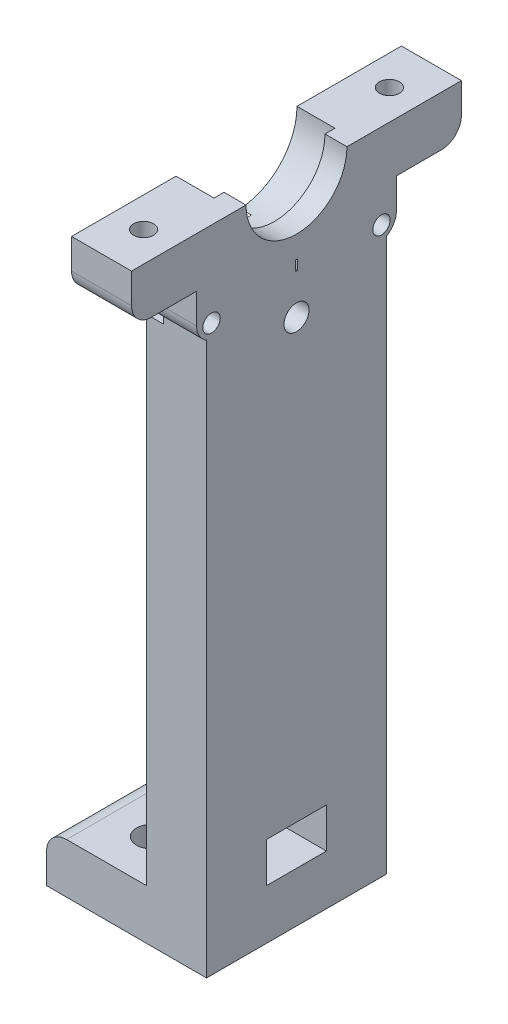
SolidWorks part; units mm, degrees
ref_plane "Front Plane" through (0, 0, 0) normal (0, 0, 1) x (1, 0, 0)
ref_plane "Top Plane" through (0, 0, 0) normal (0, 1, 0) x (1, 0, 0)
ref_plane "Right Plane" through (0, 0, 0) normal (1, 0, 0) x (0, 0, -1)
sketch "Sketch1" plane through (0, 0, 0) normal (0, 1, 0) x (1, 0, 0)
  circle A0 centre (0, 0) radius 17.45
  circle A1 centre (0, 0) radius 12.45
  dimension "D1" = 5
  dimension "D2" = 34.9
extrude "Boss-Extrude1" add sketch "Sketch1" along normal blind 8
sketch "Sketch2" plane through (0, 8, 0) normal (0, 1, 0) x (1, 0, 0)
  circle A0 centre (0, 0) radius 12.45
  circle A1 centre (0, 0) radius 20
  dimension "D1" = 40
extrude "Boss-Extrude2" add sketch "Sketch2" along normal blind 2
sketch "Sketch3" plane through (0, 10, 0) normal (0, 1, 0) x (1, 0, 0)
  circle A0 centre (0, 0) radius 12.45
  circle A1 centre (0, 0) radius 32.5
  dimension "D1" = 65
extrude "Boss-Extrude3" add sketch "Sketch3" along normal blind 4
fillet "Fillet1" radius 1 1 edges at (0, 14, 32.5)
sketch "Sketch10" plane through (0, 14, 0) normal (0, 1, 0) x (1, 0, 0)
  line L1 (30.1869, 9) -> (40.1869, 9)
  line L2 (30.1869, 9) -> (30.1869, -9)
  line L3 (30.1869, -9) -> (40.1869, -9)
  line L4 (40.1869, 9) -> (40.1869, -9)
  line L5 (-30.1869, 9) -> (-40.1869, 9)
  line L6 (-30.1869, 9) -> (-30.1869, -9)
  line L7 (-30.1869, -9) -> (-40.1869, -9)
  line L8 (-40.1869, 9) -> (-40.1869, -9)
  circle A0 centre (0, 0) radius 31.5 construction
  dimension "D1" = 10
  dimension "D2" = 18
extrude "Boss-Extrude6" add sketch "Sketch10" along normal offset from surface (4 mm away) 4 from surface at -4 up to face at (0, 10, 20) starting at face at (0, 10, 20)
sketch "Sketch4" plane through (0, 14, 0) normal (0, 1, 0) x (1, 0, 0)
  line L0 (34.1869, 0) -> (-34.1869, 0) construction
  line L2 (-34.1869, 9) -> (-34.1869, -9)
  line L8 (34.1869, 9) -> (34.1869, -9)
  line L10 (34.1869, 9) -> (40.1869, 9)
  line L11 (40.1869, 9) -> (40.1869, -9)
  line L12 (40.1869, -9) -> (34.1869, -9)
  line L13 (-34.1869, 9) -> (-40.1869, 9)
  line L14 (-40.1869, 9) -> (-40.1869, -9)
  line L15 (-40.1869, -9) -> (-34.1869, -9)
  point P8 (0, 0)
  dimension "D1" = 6
extrude "Boss-Extrude4" add sketch "Sketch4" along normal blind 75 and the other way blind 4
sketch "Sketch5" plane through (34.1869, 0, 0) normal (-1, 0, 0) x (0, 0, 1)
  line L0 (-9, 14) -> (9, 14) construction
  line L1 (-9, 89) -> (9, 89) construction
  circle A0 centre (0, 79) radius 5.05
  point P7 (0, 89)
  dimension "D1" = 10.1
  dimension "D2" = 65
extrude "Cut-Extrude1" cut sketch "Sketch5" against normal blind 113 and the other way blind 306
sketch "Sketch6" plane through (0, 0, -9) normal (0, 0, -1) x (-1, 0, 0)
  line L1 (34.1869, 75.95) -> (40.1869, 75.95)
  line L2 (34.1869, 75.95) -> (34.1869, 65.95)
  line L3 (34.1869, 65.95) -> (40.1869, 65.95)
  line L4 (40.1869, 75.95) -> (40.1869, 65.95)
  line L6 (40.1869, 89) -> (40.1869, 10) construction
  line L7 (34.1869, 14) -> (34.1869, 89) construction
  dimension "D1" = 10
  dimension "D2" = 8
extrude "Boss-Extrude5" add sketch "Sketch6" along normal blind 15 and the other way blind 32.85
sketch "Sketch7" plane through (-34.1869, 0, 0) normal (1, 0, 0) x (0, 0, -1)
  line L0 (-17.5, 71) -> (17.5, 71) construction
  circle A0 centre (-17.5, 71) radius 1.6292
  circle A1 centre (17.5, 71) radius 1.5803
  circle A3 centre (0, 79) radius 4.05 construction
  point P6 (0, 71)
  dimension "D2" = 8
  dimension "D1" = 35
  dimension "D3" = 17.5
extrude "Cut-Extrude2" cut sketch "Sketch7" against normal blind 10
sketch "Sketch9" plane through (-34.1869, 0, 0) normal (1, 0, 0) x (0, 0, -1)
  circle A0 centre (0, 79) radius 5.05
  dimension "D1" = 10.1
extrude "Cut-Extrude3" cut sketch "Sketch9" against normal blind 10 and the other way blind 10
sketch "Sketch11" plane through (34.1869, 0, 0) normal (-1, 0, 0) x (0, 0, 1)
  line L0 (-9, 14) -> (9, 14) construction
  line L1 (4.8913, 14) -> (-4.8913, 14)
  line L2 (4.8913, 14) -> (4.8913, 17.2345)
  line L3 (4.8913, 17.2345) -> (-4.8913, 17.2345)
  line L4 (-4.8913, 14) -> (-4.8913, 17.2345)
  line L5 (9, 10) -> (-9, 10) construction
  point P6 (0, 14)
  point P9 (0, 10)
extrude "Cut-Extrude4" cut sketch "Sketch11" against normal blind 61 and the other way blind 123
fillet "Fillet4" radius 3 6 edges at (-37.1869, 65.95, 23.85) (-37.1869, 75.95, 23.85) (-37.1869, 65.95, -24) (-37.1869, 75.95, -24) (-37.1869, 89, 9) (-37.1869, 89, -9)
fillet "Fillet5" radius 3 2 edges at (40.1869, 10, 0) (-40.1869, 10, 0)
sketch "Sketch12" plane through (40.1869, 0, 0) normal (1, 0, 0) x (0, 0, -1)
  line L0 (9, 10) -> (-9, 10) construction
  line L1 (41.8928, 10) -> (-66.8986, 10)
  line L2 (41.8928, 10) -> (41.8928, -14.0418)
  line L3 (41.8928, -14.0418) -> (-66.8986, -14.0418)
  line L4 (-66.8986, 10) -> (-66.8986, -14.0418)
extrude "Cut-Extrude5" cut sketch "Sketch12" against normal blind 110.678
sketch "Sketch15" plane through (0, 14, 0) normal (0, 1, 0) x (1, 0, 0)
  circle A0 centre (0, 0) radius 22
  dimension "D1" = 44
extrude "Cut-Extrude7" cut sketch "Sketch15" against normal blind 4
sketch "Sketch13" plane through (0, 14, 0) normal (0, 1, 0) x (1, 0, 0)
  line L0 (-15.1554, -8.75) -> (0, 17.5) construction
  line L1 (0, 17.5) -> (15.1554, -8.75) construction
  line L2 (15.1554, -8.75) -> (-15.1554, -8.75) construction
  circle A0 centre (0, 0) radius 11
  circle A1 centre (0, 0) radius 22
  circle A2 centre (0, 0) radius 17.5 construction
  circle A3 centre (0, 17.5) radius 2.75
  circle A4 centre (-15.1554, -8.75) radius 2.75
  circle A5 centre (15.1554, -8.75) radius 2.75
  dimension "D1" = 22
  dimension "D2" = 5.5
  dimension "D3" = 44
  dimension "D5" = 35
  dimension "D4" = 60
extrude "Boss-Extrude7" add sketch "Sketch13" against normal blind 4
fillet "Fillet6" radius 3 2 edges at (37.1869, 89, -9) (37.1869, 89, 9)
sketch "Sketch16" plane through (0, 10, 0) normal (0, -1, 0) x (1, 0, 0)
  line L0 (-31.229, 9) -> (-20.2938, 9)
  line L1 (31.229, 9) -> (20.2938, 9)
  arc A0 (-31.229, 9) -> (31.229, 9) centre (0, 0) cw
  arc A1 (-20.2938, 9) -> (20.2938, 9) centre (0, 0) cw
  dimension "D1" = 22.2
extrude "Cut-Extrude8" cut sketch "Sketch16" against normal blind 5
mirror "Mirror1" about plane through (0, 0, 0) normal (0, 0, 1) of "Cut-Extrude8"
fillet "Fillet7" radius 1 2 edges at (0, 14, 22.2) (0, 14, -22.2)
sketch "Sketch17" plane through (0, 10, 0) normal (0, -1, 0) x (1, 0, 0)
  line L0 (20.2938, -9) -> (40.1869, -9)
  line L1 (40.1869, -9) -> (40.1869, 9)
  line L2 (40.1869, 9) -> (20.2938, 9)
  arc A0 (20.2938, -9) -> (20.2938, 9) centre (0, 0) ccw
  arc A1 (-20.2938, -9) -> (20.2938, -9) centre (0, 0) ccw construction
extrude "Boss-Extrude8" add sketch "Sketch17" along normal blind 6.4 and the other way blind 3
fillet "Fillet8" radius 3 1 edges at (40.1869, 3.6, 0)
mirror "Mirror2" about plane through (0, 0, 0) normal (1, 0, 0) of "Fillet8", "Boss-Extrude8"
sketch "Sketch21" plane through (40.1869, 0, 0) normal (1, 0, 0) x (0, 0, -1)
  circle A0 centre (0, 79) radius 6.05
  dimension "D1" = 12.1
extrude "Cut-Extrude12" cut sketch "Sketch21" along normal blind 3.8 from surface at -6 starting at face at (34.1869, 79, 5.05)
sketch "Sketch18" plane through (40.1869, 0, 0) normal (1, 0, 0) x (0, 0, -1)
  line L1 (44.3735, 99.3869) -> (-44.3735, 99.3869)
  line L2 (44.3735, 99.3869) -> (44.3735, 79)
  line L3 (44.3735, 79) -> (-44.3735, 79)
  line L4 (-44.3735, 99.3869) -> (-44.3735, 79)
  circle A0 centre (0, 79) radius 5.05 construction
  point P4 (0, 79)
extrude "Cut-Extrude9" cut sketch "Sketch18" against normal blind 10
sketch "Sketch19" plane through (0, 79, 0) normal (0, 1, 0) x (1, 0, 0)
  line L0 (40.1869, -9) -> (40.1869, -5.05) construction
  line L1 (34.1869, -6.05) -> (40.1869, -6.05)
  line L2 (34.1869, -6.05) -> (34.1869, -16.5)
  line L3 (34.1869, -16.5) -> (40.1869, -16.5)
  line L4 (40.1869, -6.05) -> (40.1869, -16.5)
  line L5 (34.1869, 6.05) -> (40.1869, 6.05)
  line L6 (34.1869, 6.05) -> (34.1869, 16.5)
  line L7 (34.1869, 16.5) -> (40.1869, 16.5)
  line L8 (40.1869, 6.05) -> (40.1869, 16.5)
  dimension "D1" = 33
extrude "Boss-Extrude9" add sketch "Sketch19" against normal blind 5
fillet "Fillet9" radius 2 2 edges at (37.1869, 74, -16.5) (37.1869, 74, 16.5)
sketch "Sketch22" plane through (-34.1869, 0, 0) normal (1, 0, 0) x (0, 0, -1)
  line L1 (-15.9989, 68.4) -> (-14.4978, 71)
  line L2 (-14.4978, 71) -> (-15.9989, 73.6)
  line L3 (-15.9989, 73.6) -> (-19.0011, 73.6)
  line L4 (-19.0011, 73.6) -> (-20.5022, 71)
  line L5 (-20.5022, 71) -> (-19.0011, 68.4)
  line L6 (-19.0011, 68.4) -> (-15.9989, 68.4)
  line L7 (20.5022, 71) -> (19.0011, 73.6)
  line L8 (19.0011, 73.6) -> (15.9989, 73.6)
  line L9 (15.9989, 73.6) -> (14.4978, 71)
  line L10 (14.4978, 71) -> (15.9989, 68.4)
  line L11 (15.9989, 68.4) -> (19.0011, 68.4)
  line L12 (19.0011, 68.4) -> (20.5022, 71)
  circle A0 centre (-17.5, 71) radius 2.6 construction
  circle A1 centre (17.5, 71) radius 2.6 construction
  dimension "D1" = 5.2
extrude "Cut-Extrude13" cut sketch "Sketch22" against normal blind 2
sketch "Sketch23" plane through (0, 79, 0) normal (0, 1, 0) x (1, 0, 0)
  line L0 (37.1869, -12.3) -> (37.1869, 12.3) construction
  line L1 (34.1869, -16.5) -> (40.1869, -16.5) construction
  line L2 (34.1869, -6.05) -> (34.1869, -16.5) construction
  circle A0 centre (37.1869, -12.3) radius 1
  circle A1 centre (37.1869, 12.3) radius 1
  point P4 (37.1869, 0)
  dimension "D1" = 2
  dimension "D2" = 4.2
  dimension "D3" = 3
extrude "Cut-Extrude14" cut sketch "Sketch23" against normal blind 11
sketch "Sketch24" plane through (0, 74, 0) normal (0, -1, 0) x (1, 0, 0)
  line L1 (37.1869, 9.9906) -> (39.1869, 11.1453)
  line L2 (39.1869, 11.1453) -> (39.1869, 13.4547)
  line L3 (39.1869, 13.4547) -> (37.1869, 14.6094)
  line L4 (37.1869, 14.6094) -> (35.1869, 13.4547)
  line L5 (35.1869, 13.4547) -> (35.1869, 11.1453)
  line L6 (35.1869, 11.1453) -> (37.1869, 9.9906)
  line L7 (37.1869, -14.6094) -> (39.1869, -13.4547)
  line L8 (39.1869, -13.4547) -> (39.1869, -11.1453)
  line L9 (39.1869, -11.1453) -> (37.1869, -9.9906)
  line L10 (37.1869, -9.9906) -> (35.1869, -11.1453)
  line L11 (35.1869, -11.1453) -> (35.1869, -13.4547)
  line L12 (35.1869, -13.4547) -> (37.1869, -14.6094)
  circle A0 centre (37.1869, 12.3) radius 2 construction
  circle A1 centre (37.1869, -12.3) radius 2 construction
  dimension "D1" = 4
extrude "Cut-Extrude16" cut sketch "Sketch24" against normal blind 1.7
sketch "Sketch25" plane through (0, 0, 9) normal (0, 0, 1) x (1, 0, 0)
  line L1 (34.1869, 121.1003) -> (-54.6477, 121.1003)
  line L3 (60.9667, -34.2061) -> (-54.6477, -34.2061)
  line L4 (-54.6477, 121.1003) -> (-54.6477, -34.2061)
  line L5 (60.9667, -34.2061) -> (60.9667, 14)
  line L6 (60.9667, 14) -> (34.1869, 14)
  line L7 (34.1869, 14) -> (34.1869, 121.1003)
  line L8 (19.1948, 14) -> (34.1869, 14) construction
  line L9 (34.1869, 14) -> (34.1869, 74) construction
extrude "Cut-Extrude17" cut sketch "Sketch25" against normal blind 127 and the other way blind 55
sketch "Sketch26" plane through (34.1869, 0, 0) normal (-1, 0, 0) x (0, 0, 1)
  line L0 (-9, 14) -> (-9, 74) construction
  line L1 (9, 14) -> (-9, 14)
  line L2 (9, 14) -> (9, 19)
  line L3 (9, 19) -> (-9, 19)
  line L4 (-9, 14) -> (-9, 19)
  dimension "D1" = 5
extrude "Boss-Extrude10" add sketch "Sketch26" along normal blind 10 and the other way blind 6
fillet "Fillet10" radius 2 1 edges at (24.1869, 19, 0)
sketch "Sketch27" plane through (34.1869, 0, 0) normal (-1, 0, 0) x (0, 0, 1)
  line L0 (9, 19) -> (-9, 19) construction
  line L1 (-3, 19) -> (3, 19)
  line L2 (-3, 19) -> (-3, 23)
  line L3 (-3, 23) -> (3, 23)
  line L4 (3, 19) -> (3, 23)
  point P4 (0, 19)
  point P7 (0, 19)
  dimension "D1" = 4
  dimension "D2" = 6
extrude "Cut-Extrude18" cut sketch "Sketch27" against normal blind 10
sketch "Sketch28" plane through (0, 19, 0) normal (0, 1, 0) x (1, 0, 0)
  line L0 (30.1869, 4.5) -> (30.1869, -4.5) construction
  line L1 (24.1869, 9) -> (24.1869, -9) construction
  line L2 (40.1869, -16.5) -> (40.1869, -5.05) construction
  circle A0 centre (30.1869, 4.5) radius 1.5
  circle A1 centre (30.1869, -4.5) radius 1.5
  point P4 (30.1869, 0)
  point P7 (24.1869, 0)
  dimension "D1" = 3
  dimension "D2" = 9
  dimension "D3" = 10
extrude "Cut-Extrude19" cut sketch "Sketch28" against normal blind 10
sketch "Sketch29" plane through (34.1869, 0, 0) normal (-1, 0, 0) x (0, 0, 1)
  line L0 (-6.05, 79) -> (-10, 79)
  line L1 (-16.5, 79) -> (-6.05, 79) construction
  line L2 (-10, 79) -> (-10, 71)
  line L3 (-8, 69) -> (8, 69)
  line L4 (10, 71) -> (10, 79)
  line L5 (6.05, 79) -> (16.5, 79) construction
  line L6 (10, 79) -> (6.05, 79)
  line L7 (6.05, 79) -> (6.05, 71.9028)
  line L8 (6.05, 71.9028) -> (-6.05, 71.9028)
  line L9 (-6.05, 71.9028) -> (-6.05, 79)
  arc A0 (-8, 69) -> (-10, 71) centre (-8, 71) cw
  arc A1 (10, 71) -> (8, 69) centre (8, 71) cw
  point P16 (-10, 69)
  point P19 (10, 69)
  dimension "D3" = 2
  dimension "D1" = 20
  dimension "D2" = 10
extrude "Boss-Extrude11" add sketch "Sketch29" against normal blind 6
sketch "Sketch30" plane through (34.1869, 0, 0) normal (-1, 0, 0) x (0, 0, 1)
  line L0 (8.5, 70.5) -> (8.5, 79) construction
  line L1 (6.05, 79) -> (16.5, 79) construction
  line L2 (-8.5, 70.5) -> (8.5, 70.5) construction
  circle A0 centre (-8.5, 70.5) radius 0.87
  circle A1 centre (8.5, 70.5) radius 0.87
  point P4 (0, 70.5)
  dimension "D1" = 8.5
  dimension "D2" = 17
extrude "Cut-Extrude20" cut sketch "Sketch30" against normal blind 6
sketch "Sketch31" plane through (34.1869, 0, 0) normal (-1, 0, 0) x (0, 0, 1)
  line L1 (-7.3453, 68.5) -> (-6.1906, 70.5)
  line L2 (-6.1906, 70.5) -> (-7.3453, 72.5)
  line L3 (-7.3453, 72.5) -> (-9.6547, 72.5)
  line L4 (-9.6547, 72.5) -> (-10.8094, 70.5)
  line L5 (-10.8094, 70.5) -> (-9.6547, 68.5)
  line L6 (-9.6547, 68.5) -> (-7.3453, 68.5)
  line L7 (9.6547, 68.5) -> (10.8094, 70.5)
  line L8 (10.8094, 70.5) -> (9.6547, 72.5)
  line L9 (9.6547, 72.5) -> (7.3453, 72.5)
  line L10 (7.3453, 72.5) -> (6.1906, 70.5)
  line L11 (6.1906, 70.5) -> (7.3453, 68.5)
  line L12 (7.3453, 68.5) -> (9.6547, 68.5)
  circle A0 centre (-8.5, 70.5) radius 2 construction
  circle A1 centre (8.5, 70.5) radius 2 construction
  dimension "D1" = 4
extrude "Cut-Extrude21" cut sketch "Sketch31" against normal blind 1.7
sketch "Sketch32" plane through (34.1869, 0, 0) normal (-1, 0, 0) x (0, 0, 1)
  circle A0 centre (0, 79) radius 7.75 construction
  circle A1 centre (0, 71.25) radius 1.5
  dimension "D1" = 15.5
  dimension "D2" = 3
extrude "Cut-Extrude22" cut sketch "Sketch32" against normal blind 5
sketch "Sketch33" plane through (39.1869, 0, 0) normal (-1, 0, 0) x (0, 0, 1)
  line L1 (-0.1, 71.75) -> (0.1, 71.75)
  line L2 (-0.1, 71.75) -> (-0.1, 70.75)
  line L3 (-0.1, 70.75) -> (0.1, 70.75)
  line L4 (0.1, 71.75) -> (0.1, 70.75)
  arc A0 (-5.05, 79) -> (5.05, 79) centre (0, 79) ccw construction
  circle A2 centre (0, 71.25) radius 1.5 construction
  point P4 (0, 71.75)
  point P8 (0, 73.95)
  point P9 (-0.1, 71.25)
  dimension "D1" = 0.2
  dimension "D2" = 1
  dimension "D3" = 0
extrude "Cut-Extrude23" cut sketch "Sketch33" against normal blind 5
sketch "Sketch34" plane through (34.1869, 0, 0) normal (-1, 0, 0) x (0, 0, 1)
  circle A0 centre (0, 71.25) radius 1.755
  dimension "D1" = 3.51
extrude "Cut-Extrude24" cut sketch "Sketch34" against normal blind 1.1
sketch "Sketch35" plane through (34.1869, 0, 0) normal (-1, 0, 0) x (0, 0, 1)
  line L0 (-0.1, 70.75) -> (0.1, 70.75) construction
  circle A0 centre (0, 66.75) radius 1.25
  dimension "D2" = 4
  dimension "D1" = 2.5
extrude "Cut-Extrude25" cut sketch "Sketch35" against normal blind 11.1
